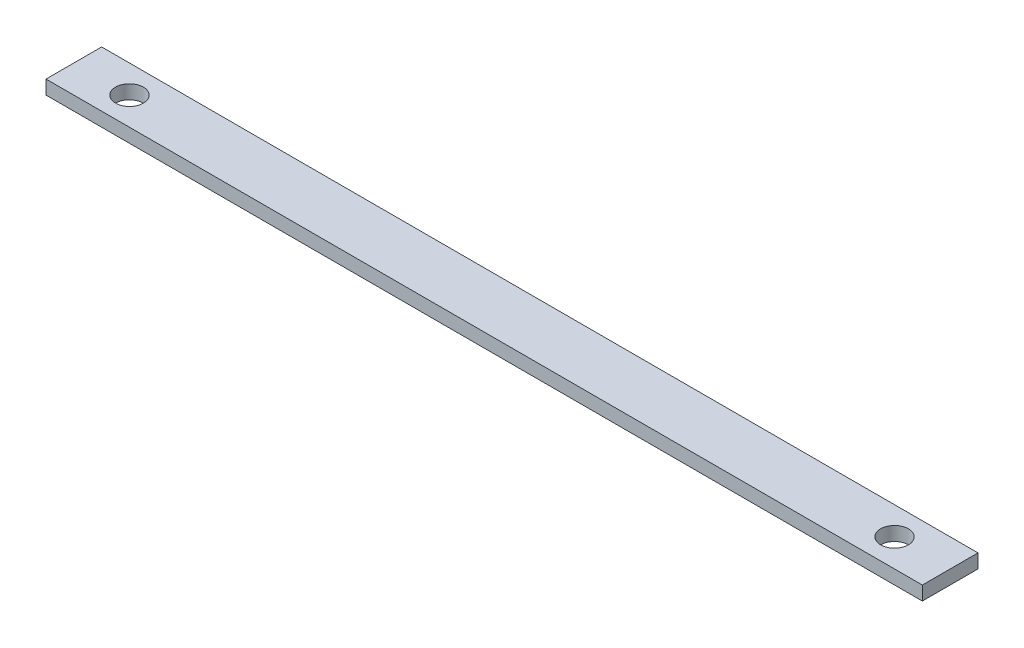
SolidWorks part; units mm, degrees
ref_plane "Front Plane" through (0, 0, 0) normal (0, 0, 1) x (1, 0, 0)
ref_plane "Top Plane" through (0, 0, 0) normal (0, 1, 0) x (1, 0, 0)
ref_plane "Right Plane" through (0, 0, 0) normal (1, 0, 0) x (0, 0, -1)
sketch "Sketch1" plane through (0, 0, 0) normal (0, 1, 0) x (1, 0, 0)
  line L1 (0, 0) -> (200, 0)
  line L2 (0, 0) -> (0, 12.7)
  line L3 (0, 12.7) -> (200, 12.7)
  line L4 (200, 0) -> (200, 12.7)
  dimension "D1" = 200
  dimension "D2" = 12.7
extrude "Boss-Extrude1" add sketch "Sketch1" along normal blind 3.175
sketch "Sketch2" plane through (0, 3.175, 0) normal (0, 1, 0) x (1, 0, 0)
  line L0 (0, 12.7) -> (0, 0) construction
  line L1 (200, 0) -> (200, 12.7) construction
  circle A0 centre (12.7, 6.35) radius 3.175
  circle A1 centre (187.3, 6.35) radius 3.175
  point P8 (0, 6.35)
  dimension "D1" = 6.35
  dimension "D2" = 12.7
  dimension "D3" = 12.7
  dimension "D4" = 6.35
extrude "Cut-Extrude1" cut sketch "Sketch2" against normal through all
